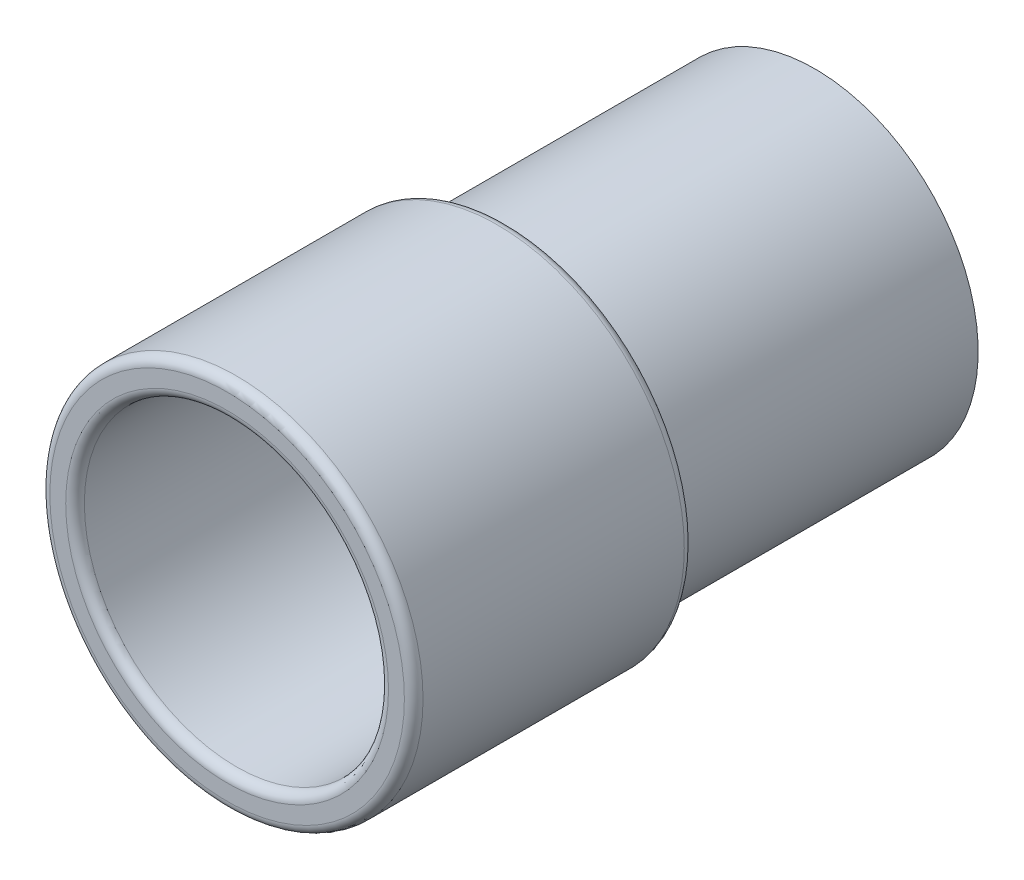
SolidWorks part; units mm, degrees
material "PVC 0.007 Plasticized"
ref_plane "Front Plane" through (0, 0, 0) normal (0, 0, 1) x (1, 0, 0)
ref_plane "Top Plane" through (0, 0, 0) normal (0, 1, 0) x (1, 0, 0)
ref_plane "Right Plane" through (0, 0, 0) normal (1, 0, 0) x (0, 0, -1)
sketch "Sketch1" plane through (0, 0, 0) normal (0, 0, 1) x (1, 0, 0)
  circle A0 centre (0, 0) radius 17.5
  circle A1 centre (0, 0) radius 15
  dimension "D1" = 35
  dimension "D2" = 30
extrude "Boss-Extrude1" add sketch "Sketch1" along normal blind 30
sketch "Sketch2" plane through (0, 0, 30) normal (0, 0, 1) x (1, 0, 0)
  circle A0 centre (0, 0) radius 16.3
  circle A3 centre (0, 0) radius 20
  dimension "D2" = 32.6
  dimension "D1" = 40
extrude "Boss-Extrude2" add sketch "Sketch2" along normal blind 30
sketch "Sketch3" plane through (0, 0, 0) normal (0, 0, -1) x (-1, 0, 0)
  circle A1 centre (0, 0) radius 17.5
  circle A2 centre (0, 0) radius 17.5
  dimension "D1" = 0
extrude "Boss-Extrude3" add sketch "Sketch3" along normal blind 3
sketch "Sketch4" plane through (0, 0, -3) normal (0, 0, -1) x (-1, 0, 0)
  line L2 (3.6546, -6.5493) -> (1.3275, -7.8479)
  line L3 (1.3275, -7.8479) -> (2.9408, -10.7392)
  line L4 (2.9408, -10.7392) -> (7.5951, -8.142)
  line L5 (7.5951, -8.142) -> (5.9817, -5.2508)
  line L6 (5.9817, -5.2508) -> (3.6546, -6.5493)
  line L7 (-3.6546, 6.5493) -> (-5.9817, 5.2508)
  line L8 (-5.9817, 5.2508) -> (-7.5951, 8.142)
  line L9 (-7.5951, 8.142) -> (-2.9408, 10.7392)
  line L10 (-2.9408, 10.7392) -> (-1.3275, 7.8479)
  line L12 (-3.6546, 6.5493) -> (-1.3245, 7.8425)
  line L13 (-1.3275, 7.8479) -> (-1.3245, 7.8425)
  line L14 (-5.268, 9.4406) -> (-8.404, 15.0607)
  point P0 (-2.1342, 9.2935)
  point P2 (6.7884, -6.6964)
  dimension "D1" = 7.5
  dimension "D2" = 7.5
  dimension "D3" = 5.3298
  dimension "D4" = 3.3109
  dimension "D5" = 3.3171
  dimension "D6" = 18.3109
extrude "Cut-Extrude1" cut sketch "Sketch4" against normal through all contours L5 L6 L2 L3 L4 | L13 L10 L9 L8 L7 L12
fillet "Fillet1" radius 0.5 8 edges at (-2.9408, -10.7392, -1.5) (-1.3275, -7.8479, -1.5) (-7.5951, -8.142, -1.5) (-5.9817, -5.2508, -1.5) (1.3245, 7.8425, -1.5) (2.9408, 10.7392, -1.5) (5.9817, 5.2508, -1.5) (7.5951, 8.142, -1.5)
sketch "Sketch5" plane through (0, 0, -3) normal (0, 0, -1) x (-1, 0, 0)
  circle A0 centre (0, 0) radius 3.5
  dimension "D1" = 7
extrude "Cut-Extrude2" cut sketch "Sketch5" against normal through all
fillet "Fillet2" radius 1 2 edges at (20, 0, 30) (20, 0, 60)
fillet "Fillet4" radius 1 3 edges at (15, 0, 0) (16.3, 0, 60) (16.3, 0, 30)
fillet "Fillet5" radius 0.5 1 edges at (15, 0, 30)
